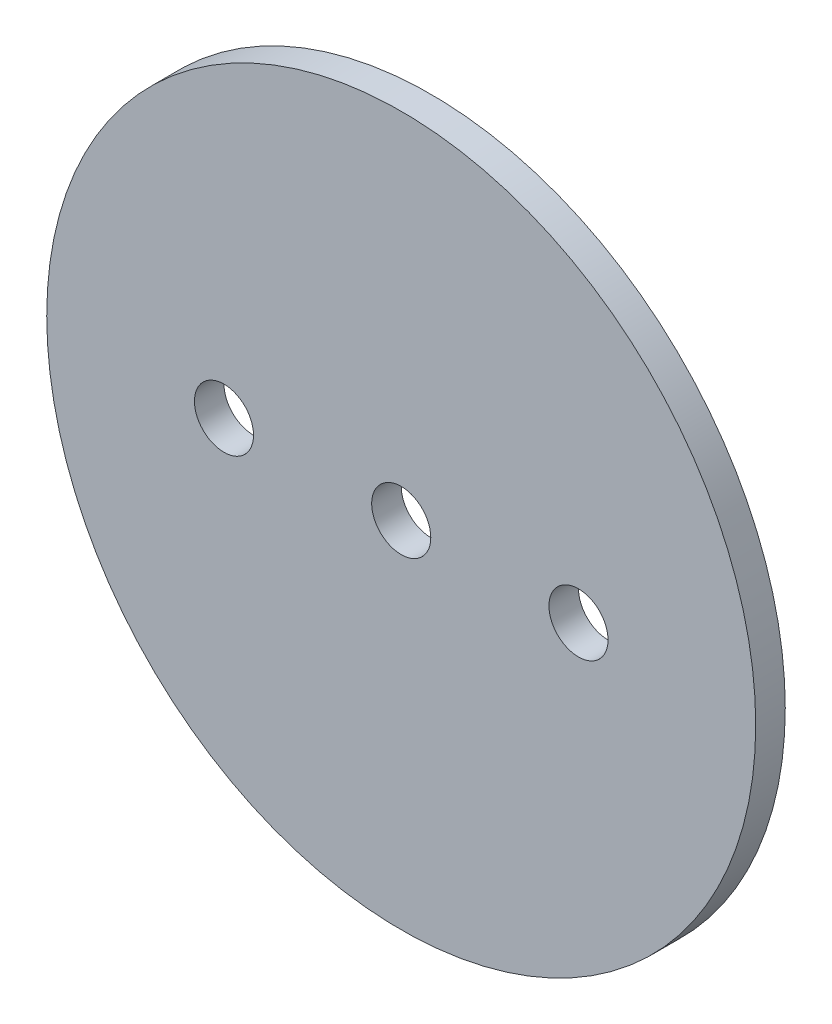
SolidWorks part; units mm, degrees
ref_plane "Front Plane" through (0, 0, 0) normal (0, 0, 1) x (1, 0, 0)
ref_plane "Top Plane" through (0, 0, 0) normal (0, 1, 0) x (1, 0, 0)
ref_plane "Right Plane" through (0, 0, 0) normal (1, 0, 0) x (0, 0, -1)
sketch "Sketch1" plane through (0, 0, 0) normal (0, 0, 1) x (1, 0, 0)
  circle A0 centre (0, 0) radius 38.1
  dimension "D1" = 76.2
extrude "Boss-Extrude1" add sketch "Sketch1" along normal mid plane 3.175
sketch "Sketch2" plane through (0, 0, 1.5875) normal (0, 0, 1) x (1, 0, 0)
  line L0 (-1000, 0) -> (49000, 0) construction
  point P1 (0, 0)
  point P4 (19.05, 0)
  point P5 (-19.05, 0)
  dimension "D1" = 19.05
  dimension "D2" = 38.1
hole_wizard "1/4 (0.25) Diameter Hole1" positions "Sketch2" profile "Sketch3" hole size "1/4" standard "ANSI Inch" end condition through all
sketch "Sketch3" plane through (-19.05, 0, 1.5875) normal (1, 0, 0) x (0, -1, 0)
  line L0 (0, 0) -> (0, 3.175)
  line L1 (0, 3.175) -> (3.175, 3.175)
  line L2 (3.175, 3.175) -> (3.175, 0)
  line L5 (3.175, 0) -> (0, 0)
  line L11 (0, -6.35) -> (0, 107.95) construction
  dimension "Thru Hole Dia." = 6.35
  dimension "Thru Hole Depth" = 3.175
equation "\"AIRFRAME_OD\"= 3.091in"
equation "\"AIRFRAME_ID\"= 3.00in"
equation "\"FLAT_T\"= 0.125in"
equation "\"NOSE_EXP_L\"= 3.5in"
equation "\"NOSE_SHOULDER_L\"= 5in"
equation "\"MAIN_L\"= 30in"
equation "\"RECO_COUP_L\"= 6in"
equation "\"RECO_SWITCH_L\"= 1.5in"
equation "\"DROGUE_L\"= 14in"
equation "\"ATS_FORE_COUP_L\"= 4in"
equation "\"ATS_AFT_COUP_L\"= 2.5in"
equation "\"LOWER_L\"= 16in"
equation "\"FIN_N\"= 4"
equation "\"CR_AFT_X\"= 0.5in"
equation "\"CR_FORE_X\"= 6in"
equation "\"FIN_ROOT\"= 5in"
equation "\"FIN_X\"= 0.75in"
equation "\"MOTOR_OD\"= 2.25in"
equation "\"MOTOR_ID\"= 2.126in"
equation "\"COUPLER_OD\"= 2.998in"
equation "\"COUPLER_ID\"= 2.875in"
equation "\"D1@Sketch1\"=\"AIRFRAME_ID\""
equation "\"D1@Boss-Extrude1\"=\"FLAT_T\""
equation "\"RECO_ROD_X\"= 1.5in"
equation "\"ATS_ROD_X\"= 2in"
equation "\"D1@Sketch2\"=\"RECO_ROD_X\"*0.5"
equation "\"D2@Sketch2\"=\"RECO_ROD_X\""
